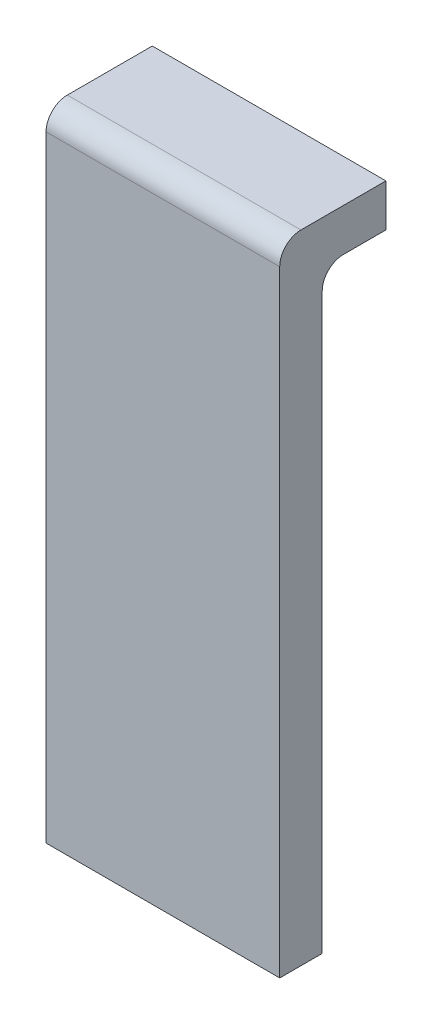
SolidWorks part; units mm, degrees
ref_plane "Plan de face" through (0, 0, 0) normal (0, 0, 1) x (1, 0, 0)
ref_plane "Plan de dessus" through (0, 0, 0) normal (0, 1, 0) x (1, 0, 0)
ref_plane "Plan de droite" through (0, 0, 0) normal (1, 0, 0) x (0, 0, -1)
sketch "Esquisse1" plane through (0, 0, 0) normal (0, 0, 1) x (1, 0, 0)
  line L1 (0, 0) -> (1.1, 0)
  line L2 (0, 0) -> (0, 3)
  line L3 (0, 3) -> (1.1, 3)
  line L4 (1.1, 0) -> (1.1, 3)
  dimension "D1" = 3
  dimension "D2" = 1.1
extrude "Boss.-Extru.1" add sketch "Esquisse1" against normal blind 0.2
sketch "Esquisse2" plane through (0, 0, -0.2) normal (0, 0, -1) x (-1, 0, 0)
  line L0 (0, 3) -> (0, 0) construction
  line L1 (-1.1, 3) -> (0, 3)
  line L2 (-1.1, 3) -> (-1.1, 2.8)
  line L3 (-1.1, 2.8) -> (0, 2.8)
  line L4 (0, 3) -> (0, 2.8)
  dimension "D1" = 0.2
extrude "Boss.-Extru.2" add sketch "Esquisse2" along normal blind 0.3
fillet "Congé1" radius 0.1 2 edges at (0.55, 3, 0)
